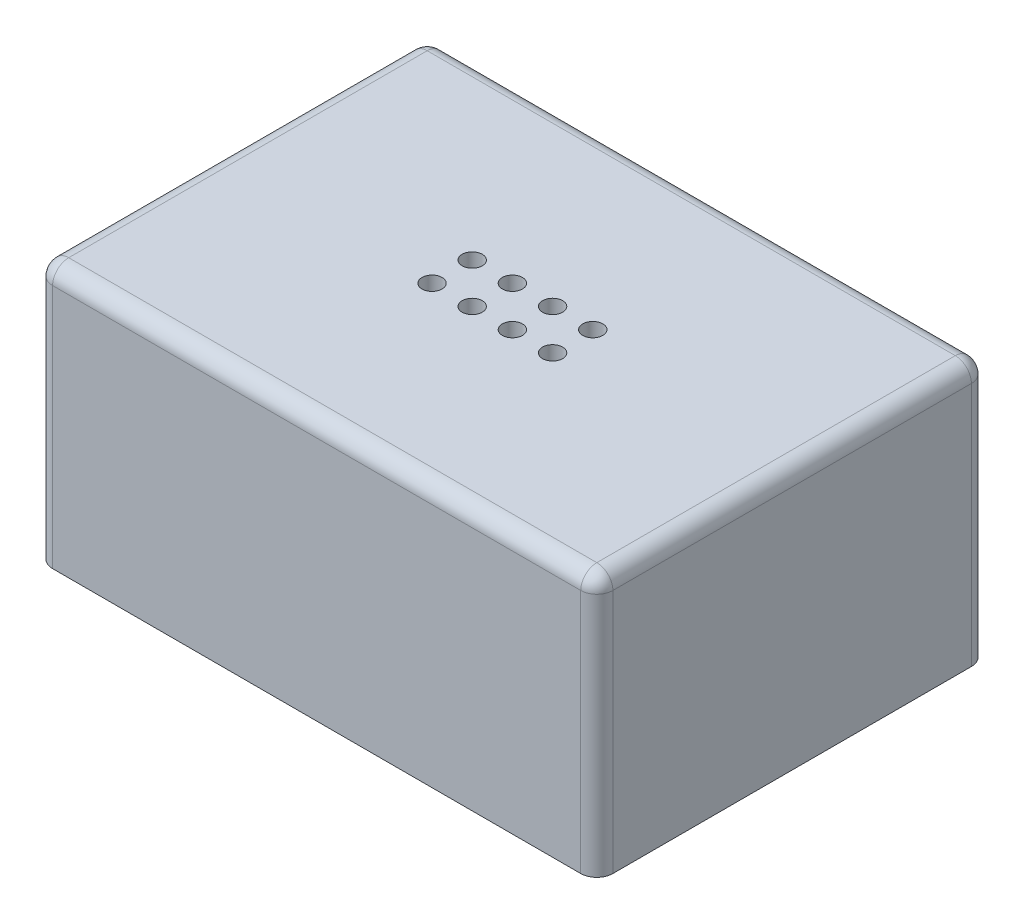
SolidWorks part; units mm, degrees
ref_plane "Front Plane" through (0, 0, 0) normal (0, 0, 1) x (1, 0, 0)
ref_plane "Top Plane" through (0, 0, 0) normal (0, 1, 0) x (1, 0, 0)
ref_plane "Right Plane" through (0, 0, 0) normal (1, 0, 0) x (0, 0, -1)
sketch "Sketch1" plane through (0, 0, 0) normal (0, 1, 0) x (1, 0, 0)
  line L1 (-42.672, 29.2735) -> (42.672, 29.2735)
  line L2 (-42.672, 29.2735) -> (-42.672, -29.2735)
  line L3 (-42.672, -29.2735) -> (42.672, -29.2735)
  line L4 (42.672, 29.2735) -> (42.672, -29.2735)
  line L5 (-42.672, 29.2735) -> (42.672, -29.2735) construction
  line L6 (-42.672, -29.2735) -> (42.672, 29.2735) construction
  point P0 (0, 0)
  point P6 (0, -29.2735)
  point P7 (0, 0)
  dimension "D1" = 85.344
  dimension "D2" = 58.547
sketch "Sketch3" plane through (0, 0, 0) normal (0, 1, 0) x (1, 0, 0)
  line L1 (-44.2595, -30.861) -> (44.2595, -30.861)
  line L2 (-44.2595, -30.861) -> (-44.2595, 30.861)
  line L3 (-44.2595, 30.861) -> (44.2595, 30.861)
  line L4 (44.2595, -30.861) -> (44.2595, 30.861)
  line L5 (-44.2595, -30.861) -> (44.2595, 30.861) construction
  line L6 (-44.2595, 30.861) -> (44.2595, -30.861) construction
  point P0 (0, 0)
  dimension "D1" = 61.722
  dimension "D2" = 88.519
extrude "Boss-Extrude2" add sketch "Sketch3" along normal blind 41.275
extrude "Cut-Extrude1" cut sketch "Sketch1" along normal blind 38.1
fillet "Fillet2" radius 2.54 8 edges at (44.2595, 20.6375, 30.861) (44.2595, 20.6375, -30.861) (-44.2595, 20.6375, -30.861) (-44.2595, 20.6375, 30.861) (0, 41.275, -30.861) (0, 41.275, 30.861) (-44.2595, 41.275, 0) (44.2595, 41.275, 0)
sketch "Sketch6" plane through (0, 41.275, 0) normal (0, 1, 0) x (1, 0, 0)
  line L0 (44.2595, 28.321) -> (44.2595, -28.321) construction
  line L1 (-41.7195, 30.861) -> (41.7195, 30.861) construction
  circle A0 centre (-9.525, -3.1115) radius 1.5875
  circle A1 centre (-3.175, -3.1115) radius 1.5875
  circle A2 centre (3.175, -3.1115) radius 1.5875
  circle A3 centre (9.525, -3.1115) radius 1.5875
  circle A4 centre (-9.525, 3.2385) radius 1.5875
  circle A5 centre (-3.175, 3.2385) radius 1.5875
  circle A6 centre (3.175, 3.2385) radius 1.5875
  circle A7 centre (9.525, 3.2385) radius 1.5875
  dimension "D1" = 3.175
  dimension "D2" = 3.175
  dimension "D3" = 3.175
  dimension "D4" = 3.175
  dimension "D5" = 3.175
  dimension "D6" = 3.175
  dimension "D7" = 3.175
  dimension "D8" = 3.175
  dimension "D9" = 6.35
  dimension "D10" = 6.35
  dimension "D11" = 6.35
  dimension "D12" = 6.35
  dimension "D13" = 34.7345
  dimension "D14" = 27.6225
extrude "Cut-Extrude4" cut sketch "Sketch6" against normal through all
fillet "Fillet3" radius 2.54 4 edges at (-42.672, 38.1, 0) (0, 38.1, 29.2735) (0, 38.1, -29.2735) (42.672, 38.1, 0)
